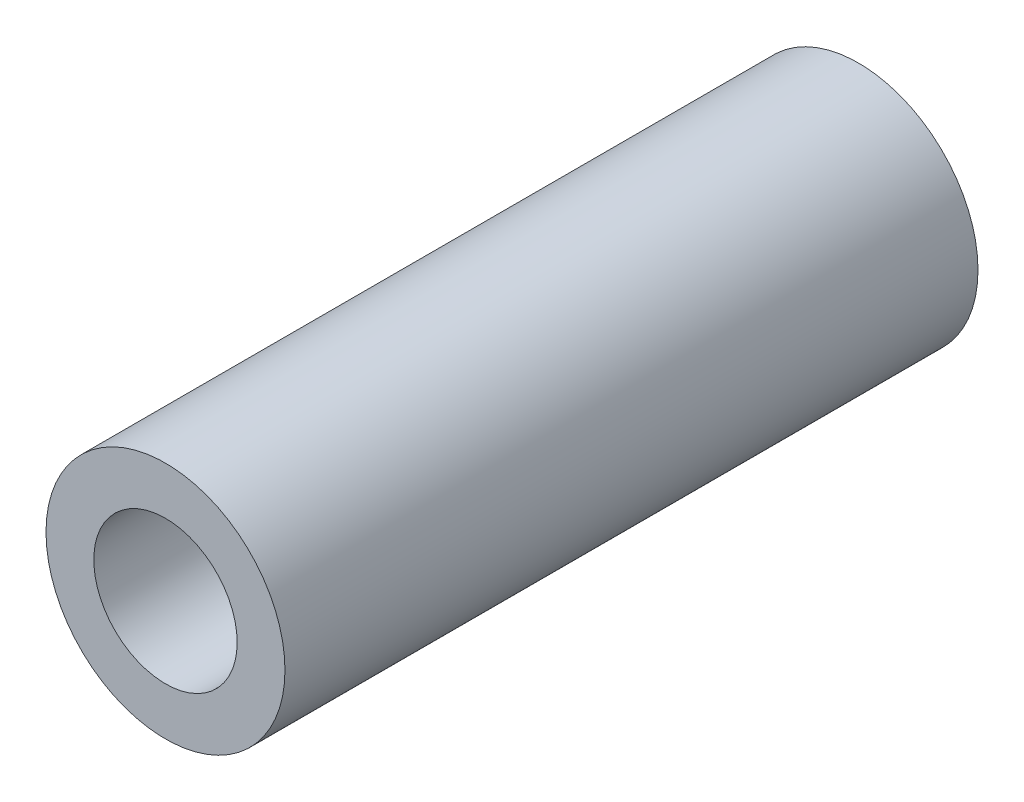
SolidWorks part; units mm, degrees
material "ﾎﾟﾘｵｷｼﾒﾁﾚﾝ(POM)ｱｾﾀｰﾙ共重合体"
ref_plane "Front Plane" through (0, 0, 0) normal (0, 0, 1) x (1, 0, 0)
ref_plane "Top Plane" through (0, 0, 0) normal (0, 1, 0) x (1, 0, 0)
ref_plane "Right Plane" through (0, 0, 0) normal (1, 0, 0) x (0, 0, -1)
sketch "Sketch2" plane through (0, 0, 0) normal (0, 0, 1) x (1, 0, 0)
  circle A0 centre (0, 0) radius 2.5
  circle A1 centre (0, 0) radius 1.5
  dimension "D1" = 3
  dimension "D2" = 5
  dimension "D3" = 5
extrude "Boss-Extrude1" add sketch "Sketch2" along normal blind 14.5
